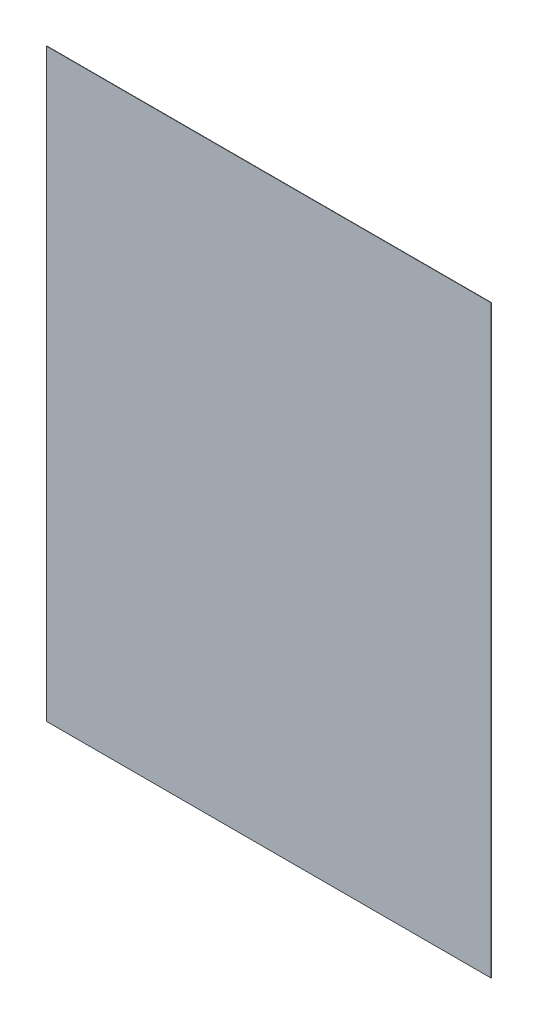
SolidWorks part; units mm, degrees
material "A123 Amp20 Negative"
ref_plane "Front Plane" through (0, 0, 0) normal (0, 0, 1) x (1, 0, 0)
ref_plane "Top Plane" through (0, 0, 0) normal (0, 1, 0) x (1, 0, 0)
ref_plane "Right Plane" through (0, 0, 0) normal (1, 0, 0) x (0, 0, -1)
sketch "Sketch1" plane through (0, 0, 0) normal (0, 0, 1) x (1, 0, 0)
  line L1 (-78.05, 102.75) -> (78.05, 102.75)
  line L2 (-78.05, 102.75) -> (-78.05, -102.75)
  line L3 (-78.05, -102.75) -> (78.05, -102.75)
  line L4 (78.05, 102.75) -> (78.05, -102.75)
  line L5 (-78.05, 102.75) -> (78.05, -102.75) construction
  line L6 (-78.05, -102.75) -> (78.05, 102.75) construction
  point P0 (0, 0)
  dimension "D1" = 156.1
  dimension "D2" = 205.5
extrude "Negative" add sketch "Sketch1" along normal blind 0.1159
